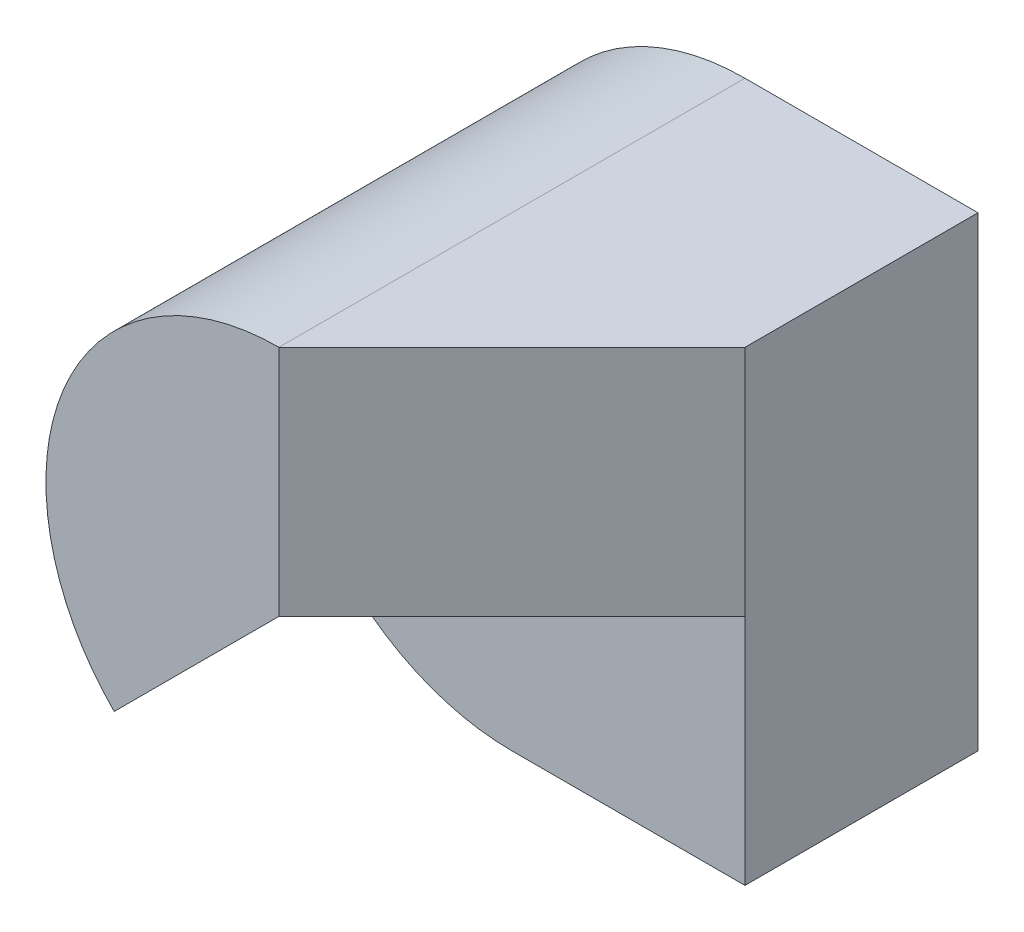
SolidWorks part; units mm, degrees
ref_plane "Front" through (0, 0, 0) normal (0, 0, 1) x (1, 0, 0)
ref_plane "Top" through (0, 0, 0) normal (0, 1, 0) x (1, 0, 0)
ref_plane "Right" through (0, 0, 0) normal (1, 0, 0) x (0, 0, -1)
sketch "Sketch1" plane through (0, 0, 0) normal (0, 0, 1) x (1, 0, 0)
  line L0 (0, 2) -> (2, 2)
  line L1 (2, 2) -> (2, -2)
  line L2 (2, -2) -> (0, -2)
  arc A0 (0, 2) -> (0, -2) centre (0, 0) ccw
  dimension "D1" = 0
  dimension "D2" = 4
  dimension "D3" = 2
extrude "Boss-Extrude1" add sketch "Sketch1" along normal blind 4
sketch "Sketch3" plane through (0, 0, 4) normal (0, 0, 1) x (1, 0, 0)
  line L0 (2, 0) -> (0, 0)
  line L1 (0, 0) -> (-2, -2)
  line L2 (-2, -2) -> (2, -2)
  line L3 (2, -2) -> (2, 0)
  point P4 (0, 0)
  point P9 (0, 0)
  dimension "D1" = 2
  dimension "D2" = 2
extrude "Cut-Extrude2" cut sketch "Sketch3" against normal blind 2
sketch3d "3DSketch2"
  line L0 (0, 0, 4) -> (2, 0, 2)
  line L1 (2, 0, 2) -> (2, 2, 2)
  line L2 (2, 2, 4) -> (2, 2, 0) construction
  line L3 (2, 2, 2) -> (0, 2, 4)
  line L4 (0, 2, 4) -> (0, 0, 4)
extrude "Cut-Extrude5" cut sketch "3DSketch2" along direction (0, 0, 1) on the side against the normal blind 2
